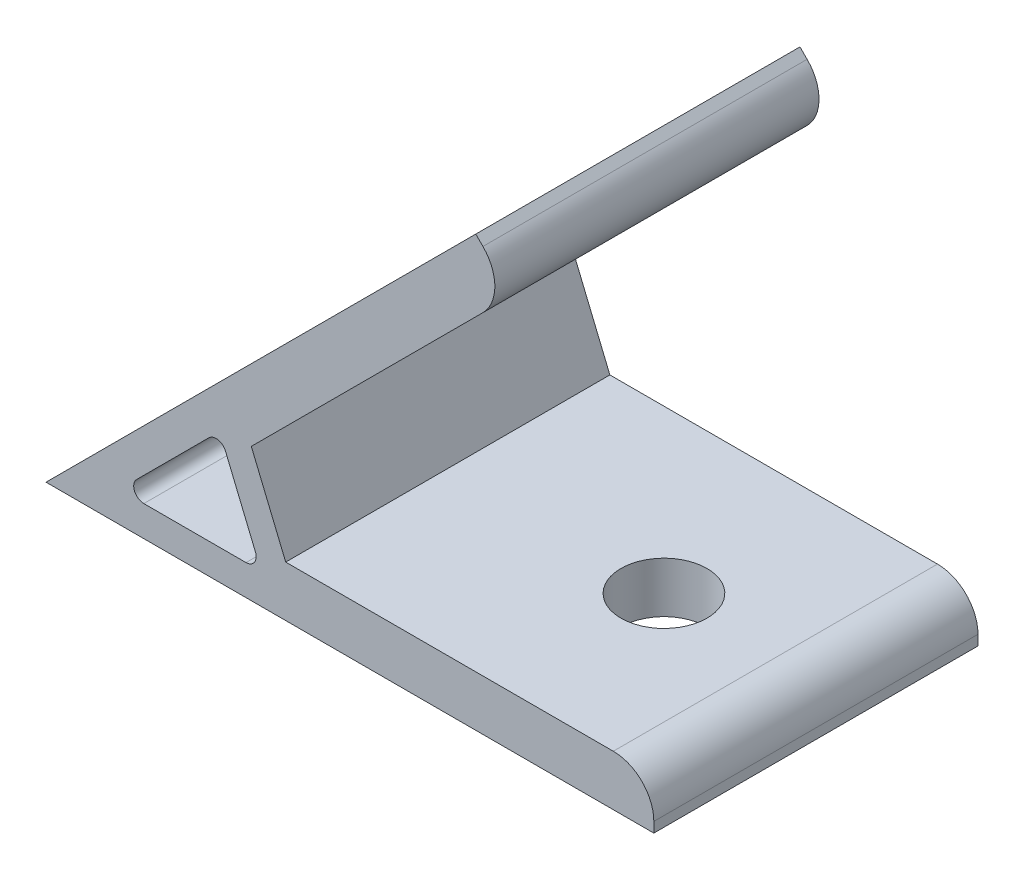
SolidWorks part; units mm, degrees
material "6063 T5"
ref_plane "Спереди" through (0, 0, 0) normal (0, 0, 1) x (1, 0, 0)
ref_plane "Сверху" through (0, 0, 0) normal (0, 1, 0) x (1, 0, 0)
ref_plane "Справа" through (0, 0, 0) normal (1, 0, 0) x (0, 0, -1)
sketch "Эскиз1" plane through (0, 0, 0) normal (0, 0, 1) x (1, 0, 0)
  line L0 (0, 0) -> (42.4264, 42.4264)
  line L1 (42.4264, 42.4264) -> (45.9619, 38.8909)
  line L2 (45.9619, 38.8909) -> (20.2667, 13.1956)
  line L3 (20.2667, 13.1956) -> (23.6614, 5)
  line L4 (23.6614, 5) -> (60, 5)
  line L5 (60, 5) -> (60, 0)
  line L6 (60, 0) -> (0, 0)
  line L7 (17.1421, 12.8995) -> (21.2426, 3)
  line L8 (21.2426, 3) -> (7.2426, 3)
  line L9 (7.2426, 3) -> (17.1421, 12.8995)
  line L10 (14.2426, 3) -> (14.2426, 0) construction
  line L11 (12.1924, 7.9497) -> (10.0711, 10.0711) construction
  line L12 (0, 0) -> (19.1924, 7.9497) construction
  point P15 (39.2751, 39.2751)
  dimension "D1" = 60
  dimension "D2" = 45
  dimension "D3" = 3
  dimension "D4" = 5
  dimension "D5" = 3
  dimension "D6" = 14
extrude "Бобышка-Вытянуть1" add sketch "Эскиз1" along normal mid plane 32
sketch "Эскиз2" plane through (0, 0, 0) normal (-0.7071, 0.7071, 0) x (0, 0, 1)
  line L0 (16, 60) -> (-16, 60) construction
  circle A0 centre (0, 45) radius 4.25
  point P2 (-2.935, 46.7791)
  dimension "D1" = 8.5
  dimension "D2" = 15
extrude "Вырез-Вытянуть1" cut sketch "Эскиз2" against normal up to surface (5 mm away) up to face at (33.1143, 26.0432, 0)
sketch "Эскиз3" plane through (0, 0, 0) normal (0, -1, 0) x (1, 0, 0)
  line L0 (60, 16) -> (60, -16) construction
  circle A0 centre (45, 0) radius 4.25
  point P2 (0, 0)
  dimension "D1" = 8.5
  dimension "D2" = 15
extrude "Вырез-Вытянуть2" cut sketch "Эскиз3" against normal up to surface (5 mm away) up to face at (41.8307, 5, 0)
fillet "Скругление1" radius 4 2 edges at (60, 5, 0) (45.9619, 38.8909, 0)
fillet "Скругление2" radius 1 3 edges at (17.1421, 12.8995, 0) (7.2426, 3, 0) (21.2426, 3, 0)
